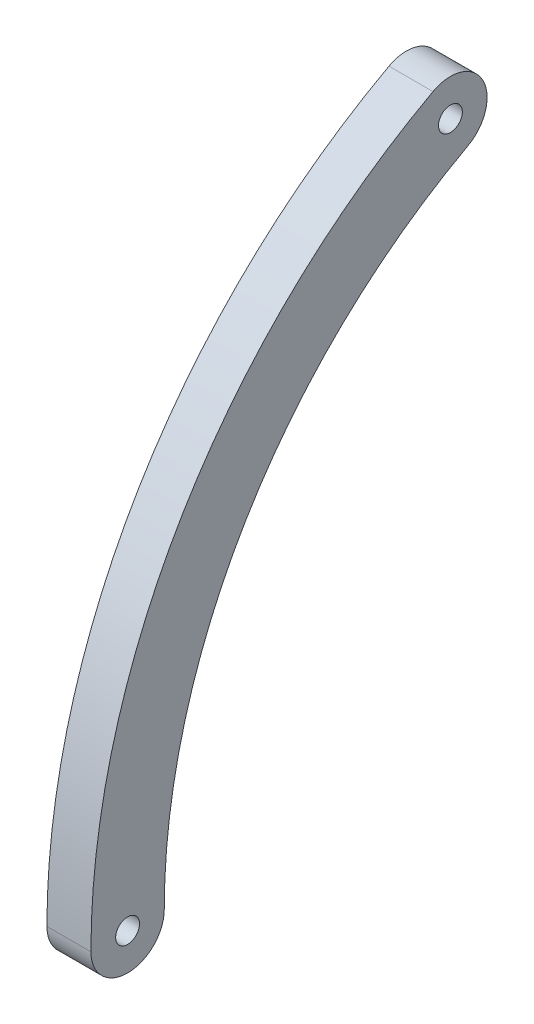
SolidWorks part; units mm, degrees
material "ABS"
ref_plane "Front Plane" through (0, 0, 0) normal (0, 0, 1) x (1, 0, 0)
ref_plane "Top Plane" through (0, 0, 0) normal (0, 1, 0) x (1, 0, 0)
ref_plane "Right Plane" through (0, 0, 0) normal (1, 0, 0) x (0, 0, -1)
sketch "Esquisse1" plane through (0, 0, 0) normal (1, 0, 0) x (0, 0, -1)
  arc A0 (-50.165, 0) -> (-23.8739, 44.1199) centre (0, 0) cw
  arc A1 (-56.515, 0) -> (-26.8959, 49.7047) centre (0, 0) cw
  arc A2 (-56.515, 0) -> (-50.165, 0) centre (-53.34, 0) ccw
  arc A3 (-23.8739, 44.1199) -> (-26.8959, 49.7047) centre (-25.3849, 46.9123) ccw
  circle A4 centre (-53.34, 0) radius 1.0319
  circle A5 centre (-25.3849, 46.9123) radius 1.0319
  dimension "D1" = 3.175
  dimension "D4" = 2.0638
  dimension "D5" = 2.0638
  dimension "D2" = 54.61
  dimension "D3" = 53.34
extrude "Boss.-Extru.1" add sketch "Esquisse1" along normal blind 3.81
